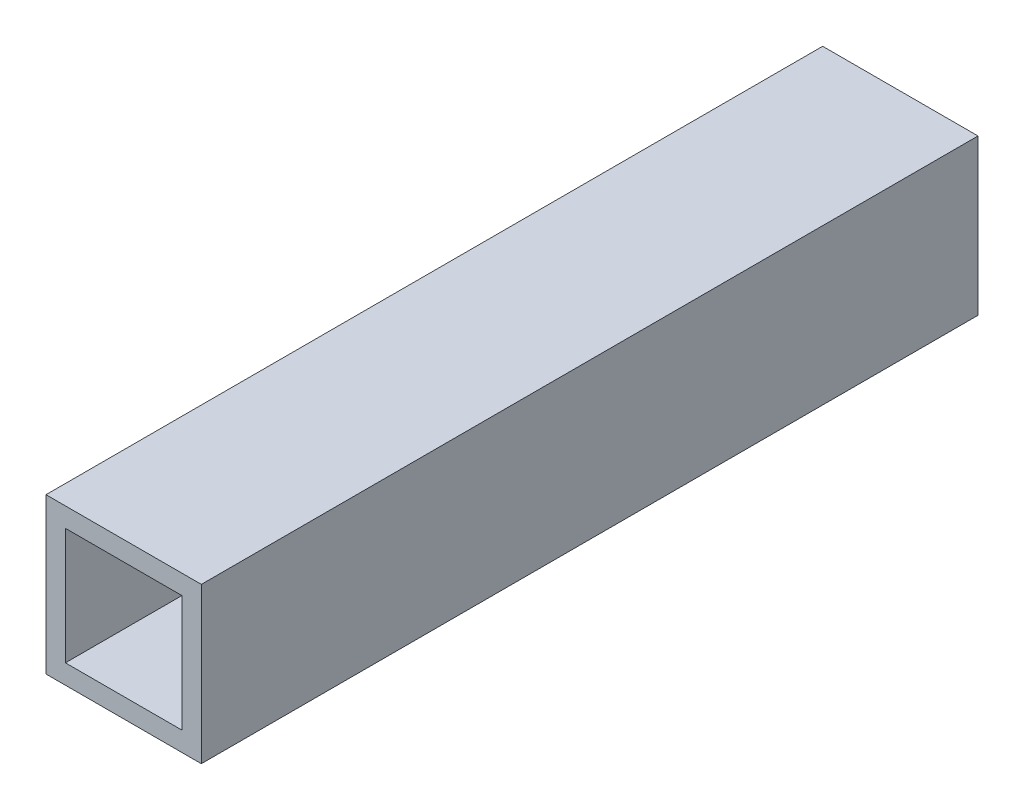
SolidWorks part; units mm, degrees
ref_plane "Front Plane" through (0, 0, 0) normal (0, 0, 1) x (1, 0, 0)
ref_plane "Top Plane" through (0, 0, 0) normal (0, 1, 0) x (1, 0, 0)
ref_plane "Right Plane" through (0, 0, 0) normal (1, 0, 0) x (0, 0, -1)
sketch "Sketch1" plane through (0, 0, 0) normal (0, 0, 1) x (1, 0, 0)
  line L1 (-12.7, -12.7) -> (12.7, -12.7)
  line L2 (-12.7, -12.7) -> (-12.7, 12.7)
  line L3 (-12.7, 12.7) -> (12.7, 12.7)
  line L4 (12.7, -12.7) -> (12.7, 12.7)
  line L5 (-12.7, -12.7) -> (12.7, 12.7) construction
  line L6 (-12.7, 12.7) -> (12.7, -12.7) construction
  point P0 (0, 0)
  dimension "D1" = 25.4
  dimension "D2" = 25.4
extrude "Boss-Extrude1" add sketch "Sketch1" along normal mid plane 127
shell "Shell1" thickness 3.175
